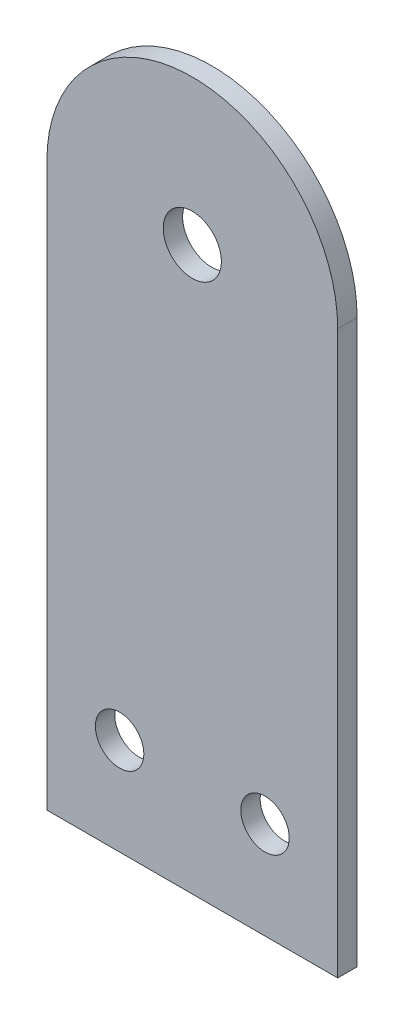
SolidWorks part; units mm, degrees
ref_plane "Ön Düzlem" through (0, 0, 0) normal (0, 0, 1) x (1, 0, 0)
ref_plane "Üst Düzlem" through (0, 0, 0) normal (0, 1, 0) x (1, 0, 0)
ref_plane "Sağ Düzlem" through (0, 0, 0) normal (1, 0, 0) x (0, 0, -1)
sketch "Sketch1" plane through (0, 0, 0) normal (0, 0, 1) x (1, 0, 0)
  line L0 (0, 0) -> (30, 0)
  line L1 (30, 0) -> (30, 58)
  line L2 (0, 58) -> (0, 0)
  arc A0 (30, 58) -> (0, 58) centre (15, 58) ccw
  dimension "D1" = 58
  dimension "D2" = 30
extrude "Boss-Extrude1" add sketch "Sketch1" along normal blind 2
sketch "Sketch2" plane through (0, 0, 2) normal (0, 0, 1) x (1, 0, 0)
  line L0 (0, 0) -> (30, 0) construction
  line L1 (0, 58) -> (0, 0) construction
  circle A0 centre (7.5, 10) radius 2.5
  circle A1 centre (15, 58) radius 3
  circle A2 centre (22.5, 10) radius 2.5
  dimension "D1" = 5
  dimension "D5" = 6
  dimension "D2" = 10
  dimension "D3" = 15
  dimension "D4" = 7.5
extrude "Cut-Extrude1" cut sketch "Sketch2" against normal blind 2
